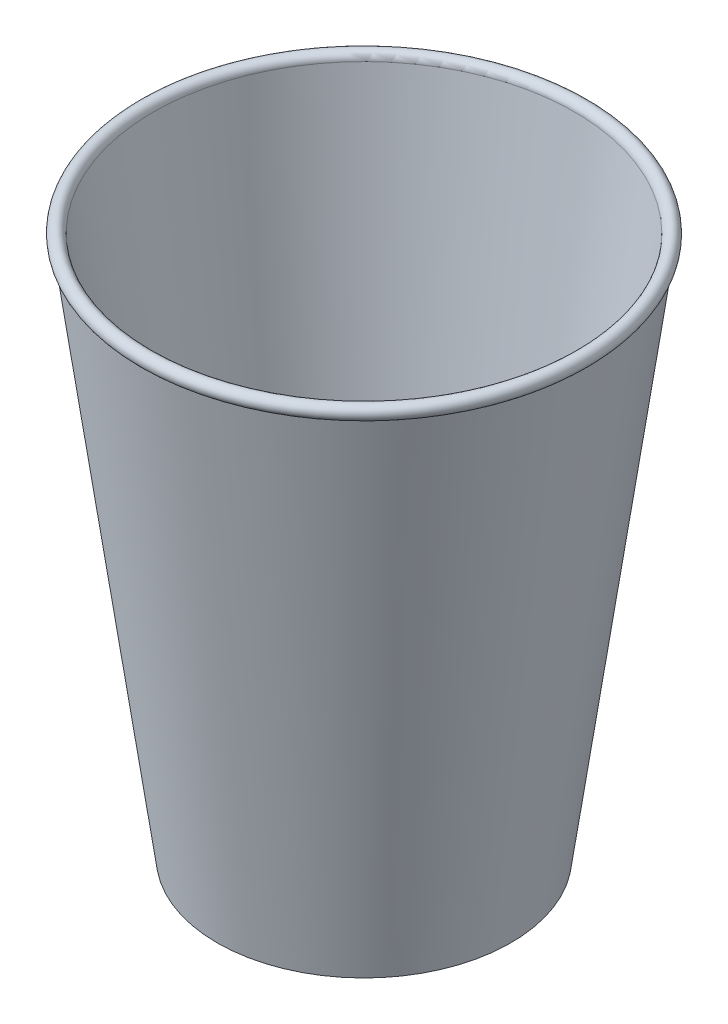
SolidWorks part; units mm, degrees
ref_plane "Front Plane" through (0, 0, 0) normal (0, 0, 1) x (1, 0, 0)
ref_plane "Top Plane" through (0, 0, 0) normal (0, 1, 0) x (1, 0, 0)
ref_plane "Right Plane" through (0, 0, 0) normal (1, 0, 0) x (0, 0, -1)
sketch "Sketch2" plane through (0, 0, 0) normal (0, 0, 1) x (1, 0, 0)
  line L0 (0, -60.6735) -> (-29.5, -60.6735)
  line L1 (0, -55) -> (0, 55) construction
  line L2 (-29.5, -60.6735) -> (-44.1299, 46.6121)
  line L3 (-42.2871, -40.6735) -> (-27.7542, -40.6735) construction
  line L4 (-42.2871, 47.9008) -> (-27.7542, -58.6735)
  line L5 (-27.7542, -58.6735) -> (0, -58.6735)
  line L6 (0, -58.6735) -> (0, -60.6735)
  line L7 (0, 29.1882) -> (0, -40.6735) construction
  line L8 (-48.3933, 9.3265) -> (-30.4406, 9.3265) construction
  line L9 (-32.2271, -46.2447) -> (-32.2271, -35.6578) construction
  line L10 (-39.0454, 9.0243) -> (-39.0454, 9.8111) construction
  arc A0 (-42.2871, 47.9008) -> (-44.1299, 46.6121) centre (-43.6841, 47.9366) ccw
  dimension "D1" = 2
  dimension "D2" = 29.5
  dimension "D3" = 2
  dimension "D4" = 50
  dimension "D5" = 20
revolve "Revolve1" add sketch "Sketch2" angle 360 about L7
